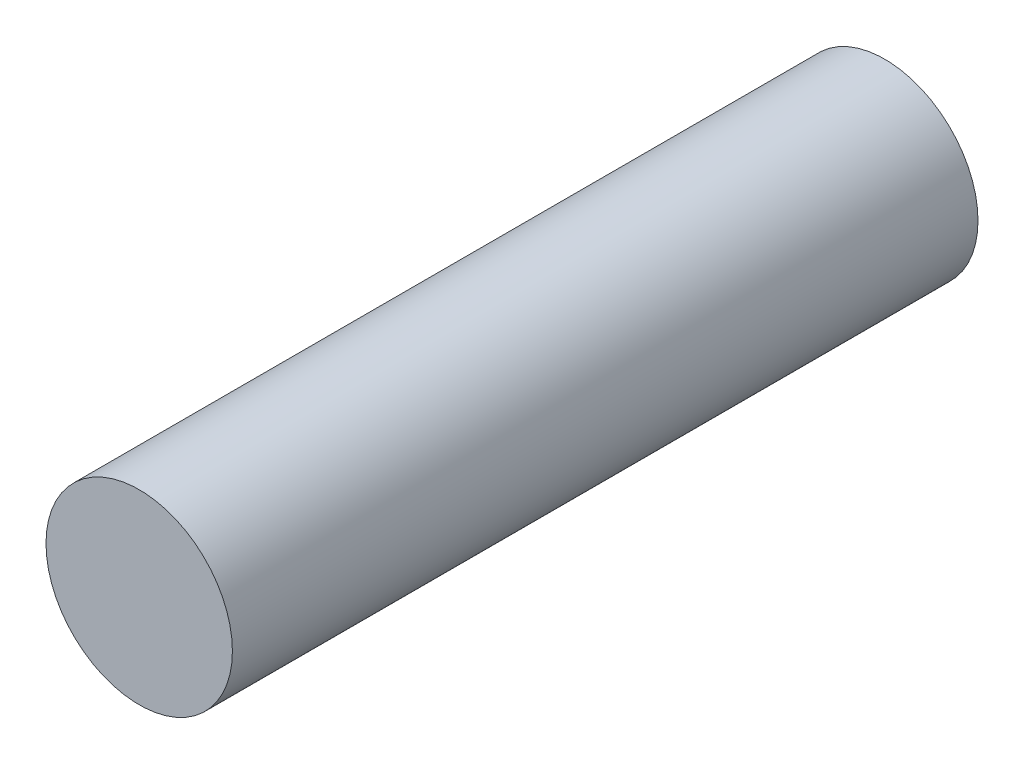
SolidWorks part; units mm, degrees
ref_plane "Front" through (0, 0, 0) normal (0, 0, 1) x (1, 0, 0)
ref_plane "Top" through (0, 0, 0) normal (0, 1, 0) x (1, 0, 0)
ref_plane "Right" through (0, 0, 0) normal (1, 0, 0) x (0, 0, -1)
sketch "Sketch1" plane through (0, 0, 0) normal (0, 0, 1) x (1, 0, 0)
  circle A0 centre (0, 0) radius 4.7625
  dimension "D1" = 9.525
extrude "Base-Extrude" add sketch "Sketch1" along normal blind 38.1
